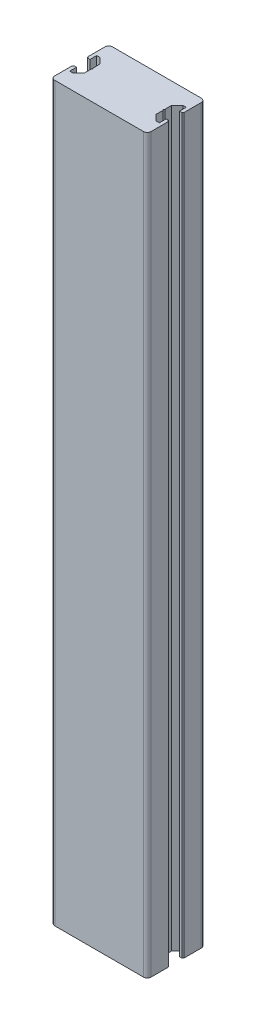
SolidWorks part; units mm, degrees
ref_plane "Front Plane" through (0, 0, 0) normal (0, 0, 1) x (1, 0, 0)
ref_plane "Top Plane" through (0, 0, 0) normal (0, 1, 0) x (1, 0, 0)
ref_plane "Right Plane" through (0, 0, 0) normal (1, 0, 0) x (0, 0, -1)
sketch "Sketch1" plane through (0, 0, 0) normal (0, 1, 0) x (1, 0, 0)
  line L0 (0, 17.25) -> (2.625, 17.25)
  line L5 (0, 0) -> (75, 0)
  line L6 (0, 0) -> (0, 45)
  line L7 (0, 45) -> (75, 45)
  line L8 (75, 0) -> (75, 45)
  line L9 (2.625, 17.25) -> (2.625, 12)
  line L10 (2.625, 12) -> (5.25, 12)
  line L11 (5.25, 12) -> (9.625, 16.375)
  line L12 (9.625, 16.375) -> (9.625, 28.625)
  line L13 (9.625, 28.625) -> (5.25, 33)
  line L14 (5.25, 33) -> (2.625, 33)
  line L15 (2.625, 33) -> (2.625, 27.75)
  line L16 (2.625, 27.75) -> (0, 27.75)
  line L17 (0, 27.75) -> (0, 17.25)
  line L18 (37.5, 45) -> (37.5, 0) construction
  line L19 (72.375, 27.75) -> (75, 27.75)
  line L20 (72.375, 33) -> (72.375, 27.75)
  line L21 (69.75, 33) -> (72.375, 33)
  line L22 (65.375, 28.625) -> (69.75, 33)
  line L23 (65.375, 16.375) -> (65.375, 28.625)
  line L24 (69.75, 12) -> (65.375, 16.375)
  line L25 (72.375, 12) -> (69.75, 12)
  line L26 (72.375, 17.25) -> (72.375, 12)
  line L27 (75, 17.25) -> (72.375, 17.25)
  line L28 (75, 27.75) -> (75, 17.25)
  line L29 (0, 17.25) -> (0.75, 17.25)
  line L30 (0, 16.5) -> (0, 17.25)
  line L31 (0, 27.75) -> (0.75, 27.75)
  line L32 (0, 28.5) -> (0, 27.75)
  line L33 (75, 16.5) -> (75, 17.25)
  line L34 (75, 17.25) -> (74.25, 17.25)
  line L35 (75, 28.5) -> (75, 27.75)
  line L36 (75, 27.75) -> (74.25, 27.75)
  line L37 (9.625, 23.25) -> (10.375, 22.5)
  line L38 (10.375, 22.5) -> (9.625, 21.75)
  line L39 (9.625, 21.75) -> (9.625, 23.25)
  line L40 (64.625, 22.5) -> (65.375, 21.75)
  line L41 (65.375, 23.25) -> (64.625, 22.5)
  line L42 (65.375, 21.75) -> (65.375, 23.25)
  arc A0 (0.75, 27.75) -> (0, 28.5) centre (0, 27.75) ccw
  arc A1 (0.75, 17.25) -> (0, 16.5) centre (0, 17.25) cw
  arc A2 (74.25, 17.25) -> (75, 16.5) centre (75, 17.25) ccw
  arc A3 (74.25, 27.75) -> (75, 28.5) centre (75, 27.75) cw
  point P8 (9.625, 22.5)
  point P17 (0, 22.5)
  dimension "D9" = 0.75
  dimension "D10" = 0.75
  dimension "D1" = 45
  dimension "D2" = 75
  dimension "D3" = 10.5
  dimension "D4" = 12.25
  dimension "D5" = 9.625
  dimension "D6" = 2.625
  dimension "D7" = 2.625
  dimension "D8" = 21
  dimension "D11" = 0.75
  dimension "D12" = 0.75
  dimension "D13" = 0.75
extrude "Boss-Extrude1" add sketch "Sketch1" along normal blind 570 contours L18 L7 L6 A0 L16 L15 L14 L13 L12 L37 L38 L11 L10 L9 L0 A1 L5 | L7 L18 L5 L8 A2 L27 L26 L25 L24 L23 L40 L41 L22 L21 L20 L19 A3
fillet "Fillet1" radius 3 4 edges at (75, 285, 0) (0, 285, 0) (0, 285, -45) (75, 285, -45)
sketch "Sketch2" plane through (0, 0, -45) normal (0, 0, -1) x (-1, 0, 0)
  line L1 (-3, 0) -> (-3, 570) construction
  line L2 (-72, 570) -> (-72, 0) construction
  line L5 (-3, 0) -> (-72, 0) construction
  line L6 (-3, 570) -> (-72, 570) construction
  circle A0 centre (-6.5, 48) radius 1.5
  circle A1 centre (-6.5, 8) radius 1.5
  circle A2 centre (-68.5, 48) radius 1.5
  circle A3 centre (-68.5, 8) radius 1.5
  circle A12 centre (-68.5, 562) radius 1.5
  circle A13 centre (-68.5, 522) radius 1.5
  circle A14 centre (-68.5, 462) radius 1.5
  circle A15 centre (-68.5, 422) radius 1.5
  circle A16 centre (-68.5, 362) radius 1.5
  circle A17 centre (-68.5, 322) radius 1.5
  circle A18 centre (-6.5, 362) radius 1.5
  circle A19 centre (-6.5, 322) radius 1.5
  point P32 (-68.7964, 346.764)
  point P33 (-68.7964, 415.7358)
  point P34 (0, 0)
  point P35 (0, 0)
  point P36 (0, 0)
  dimension "D1" = 3
  dimension "D2" = 40
  dimension "D6" = 3
  dimension "D3" = 8
  dimension "D4" = 3.5
  dimension "D5" = 3.5
  dimension "D7" = 8
  dimension "D8" = 40
  dimension "D9" = 40
  dimension "D10" = 40
  dimension "D11" = 60
  dimension "D12" = 60
  dimension "D13" = 40
  dimension "D14" = 3.5
  dimension "D15" = 3.5
extrude "Cut-Extrude1" cut sketch "Sketch2" against normal blind 10
